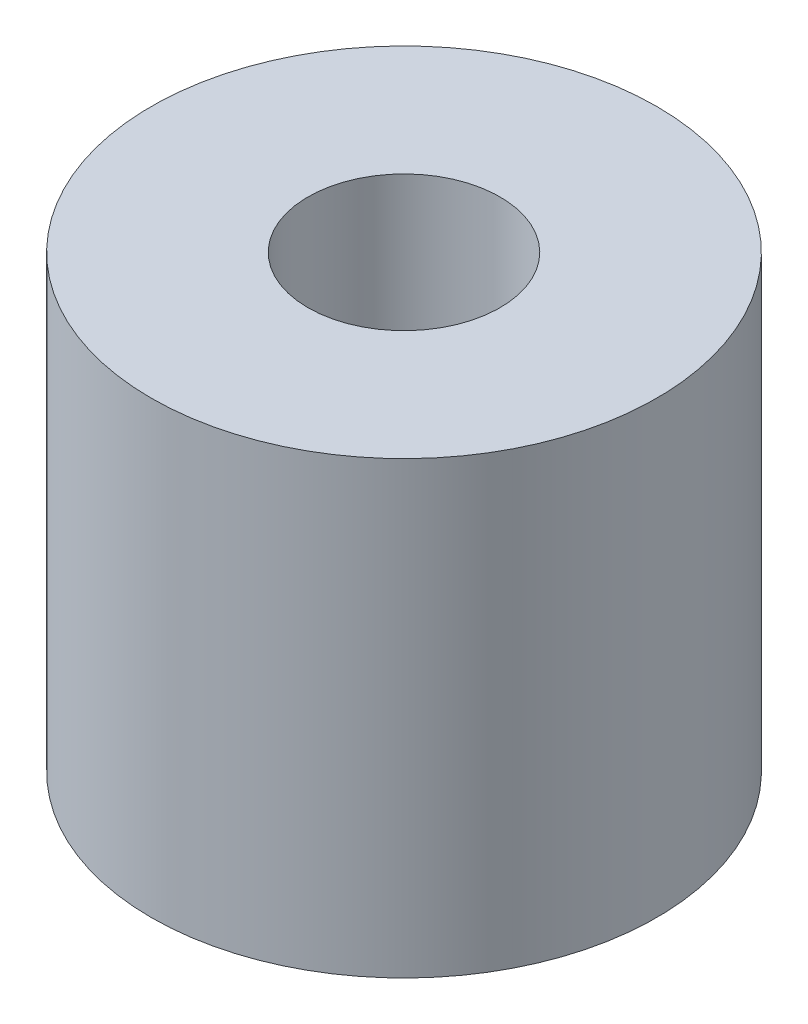
SolidWorks part; units mm, degrees
ref_plane "Front Plane" through (0, 0, 0) normal (0, 0, 1) x (1, 0, 0)
ref_plane "Top Plane" through (0, 0, 0) normal (0, 1, 0) x (1, 0, 0)
ref_plane "Right Plane" through (0, 0, 0) normal (1, 0, 0) x (0, 0, -1)
sketch "Sketch1" plane through (0, 0, 0) normal (0, 1, 0) x (1, 0, 0)
  circle A0 centre (0, 0) radius 4.826
  circle A1 centre (0, 0) radius 12.7
  dimension "D1" = 9.652
  dimension "D2" = 25.4
extrude "Boss-Extrude1" add sketch "Sketch1" along normal blind 22.606
